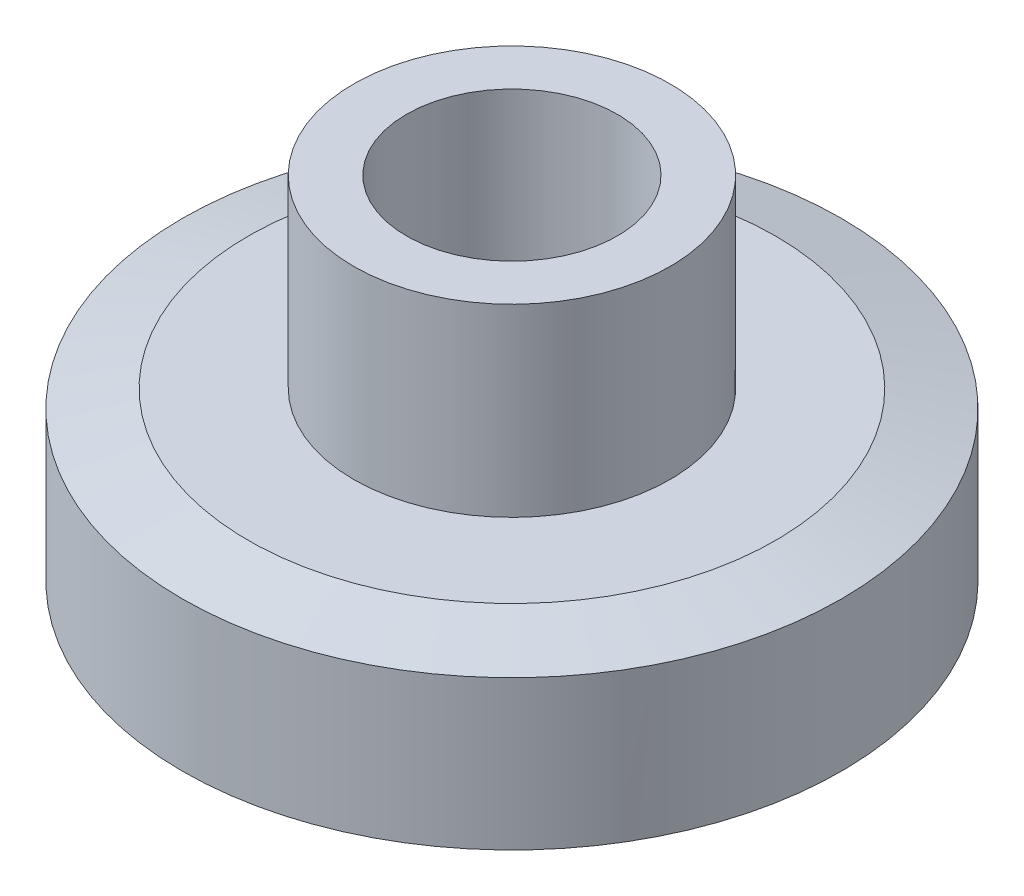
SolidWorks part; units mm, degrees
material "Сталь ШХ15 ГОСТ 801-78"
ref_plane "Plane1" through (0, 0, 0) normal (0, 0, 1) x (1, 0, 0)
ref_plane "Plane2" through (0, 0, 0) normal (0, 1, 0) x (1, 0, 0)
ref_plane "Plane3" through (0, 0, 0) normal (1, 0, 0) x (0, 0, -1)
sketch "Эскиз2" plane through (0, 0, 0) normal (0, 0, 1) x (1, 0, 0)
  line L0 (0, 0) -> (6.25, 0)
  line L1 (6.25, 0) -> (6.25, 3.5)
  line L2 (6.25, 3.5) -> (3, 3.5)
  line L3 (3, 3.5) -> (3, 7)
  line L4 (3, 7) -> (0, 7)
  line L5 (0, 7) -> (0, 0)
  dimension "D1" = 6.25
  dimension "D2" = 3.5
  dimension "D3" = 3.5
  dimension "D4" = 3
ref_axis "Ось1" through (0, 7, 0) along (0, -1, 0)
revolve "Повернуть2" add sketch "Эскиз2" angle 360 about axis through (0, 7, 0) along (0, -1, 0)
chamfer "Фаска2" distance 1.25 angle 15 1 edges at (0, 3.5, 6.25)
chamfer "Фаска3" distance 1.25 angle 15 1 edges at (0, 0, 6.25)
sketch "Эскиз4" plane through (0, 7, 0) normal (0, 1, 0) x (1, 0, 0)
  circle A0 centre (0, 0) radius 2
  dimension "D1" = 4
extrude "Вырез-Вытянуть2" cut sketch "Эскиз4" against normal through all both contours A0
